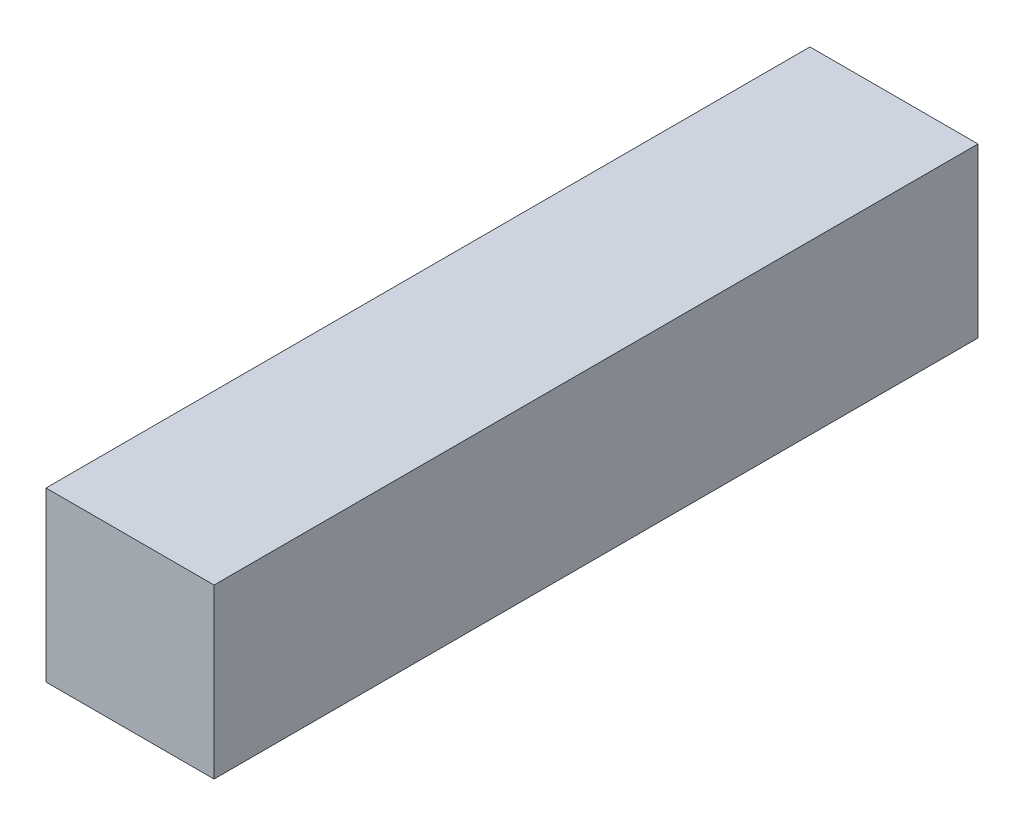
SolidWorks part; units mm, degrees
ref_plane "Plan de face" through (0, 0, 0) normal (0, 0, 1) x (1, 0, 0)
ref_plane "Plan de dessus" through (0, 0, 0) normal (0, 1, 0) x (1, 0, 0)
ref_plane "Plan de droite" through (0, 0, 0) normal (1, 0, 0) x (0, 0, -1)
sketch "Esquisse1" plane through (0, 0, 0) normal (0, 0, 1) x (1, 0, 0)
  line L1 (-11, 11) -> (11, 11)
  line L2 (-11, 11) -> (-11, -11)
  line L3 (-11, -11) -> (11, -11)
  line L4 (11, 11) -> (11, -11)
  line L5 (-11, 11) -> (11, -11) construction
  line L6 (-11, -11) -> (11, 11) construction
  point P0 (0, 0)
  dimension "D1" = 22
  dimension "D2" = 22
extrude "Boss.-Extru.1" add sketch "Esquisse1" along normal blind 100
